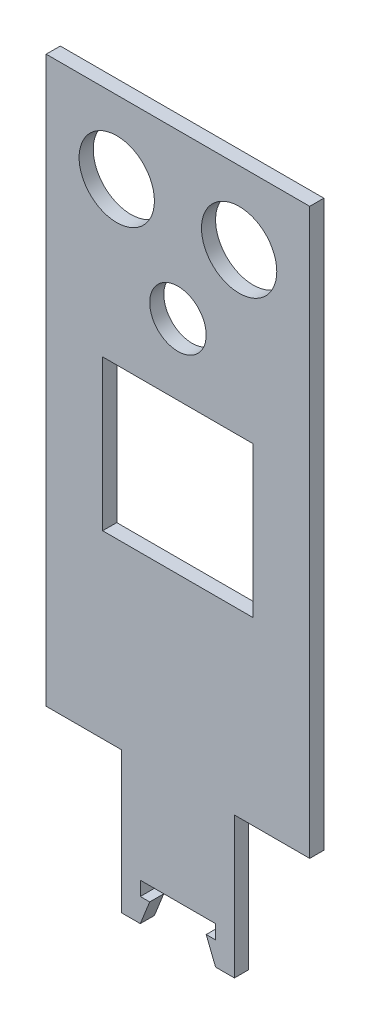
SolidWorks part; units mm, degrees
ref_plane "Alzado" through (0, 0, 0) normal (0, 0, 1) x (1, 0, 0)
ref_plane "Planta" through (0, 0, 0) normal (0, 1, 0) x (1, 0, 0)
ref_plane "Vista lateral" through (0, 0, 0) normal (1, 0, 0) x (0, 0, -1)
sketch "Model" plane through (0, 0, 0) normal (0, 0, 1) x (1, 0, 0)
  line L0 (18.5825, 92.133) -> (18.5825, -27.867)
  line L1 (2.5825, -27.867) -> (18.5825, -27.867)
  line L2 (2.5825, -57.867) -> (2.5825, -27.867)
  line L3 (-1.4175, -57.867) -> (2.5825, -57.867)
  line L4 (-3.4175, -52.867) -> (-1.4175, -57.867)
  line L5 (-1.4175, -52.867) -> (-3.4175, -52.867)
  line L6 (-1.4175, -49.867) -> (-1.4175, -52.867)
  line L7 (-17.4175, -49.867) -> (-1.4175, -49.867)
  line L8 (-17.4175, -52.867) -> (-17.4175, -49.867)
  line L9 (-15.4175, -52.867) -> (-17.4175, -52.867)
  line L10 (-17.4175, -57.867) -> (-15.4175, -52.867)
  line L11 (-21.4175, -57.867) -> (-17.4175, -57.867)
  line L12 (-21.4175, -27.867) -> (-21.4175, -57.867)
  line L13 (-37.4175, -27.867) -> (-21.4175, -27.867)
  line L14 (-37.4175, 92.133) -> (-37.4175, -27.867)
  line L15 (18.5825, 92.133) -> (-37.4175, 92.133)
  line L16 (6.5825, 42.433) -> (6.5825, 10.433)
  line L17 (-25.4175, 42.433) -> (6.5825, 42.433)
  line L18 (-25.4175, 10.433) -> (-25.4175, 42.433)
  line L19 (6.5825, 10.433) -> (-25.4175, 10.433)
  circle A0 centre (-9.4175, 57.433) radius 6
  circle A1 centre (-22.4175, 76.633) radius 8
  circle A2 centre (3.5825, 76.633) radius 8
extrude "Saliente-Extruir1" add sketch "Model" along normal blind 3
